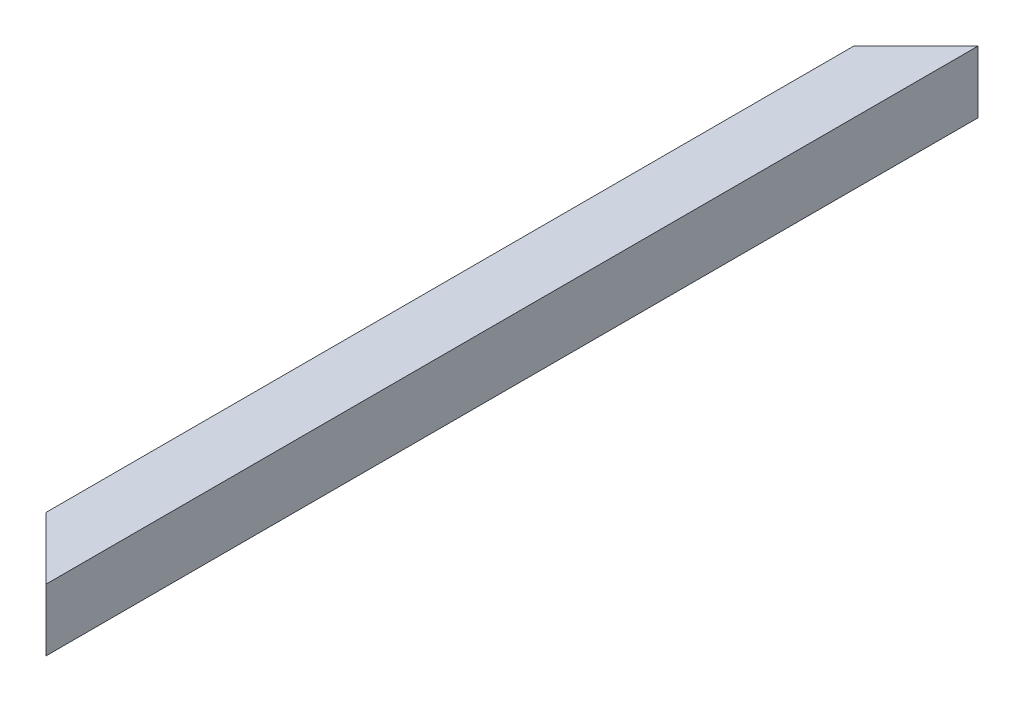
SolidWorks part; units mm, degrees
ref_plane "Front Plane" through (0, 0, 0) normal (0, 0, 1) x (1, 0, 0)
ref_plane "Top Plane" through (0, 0, 0) normal (0, 1, 0) x (1, 0, 0)
ref_plane "Right Plane" through (0, 0, 0) normal (1, 0, 0) x (0, 0, -1)
curve "Curve1"
  spline degree 1 poles (0, 0, 0) (0, 0, 900) knots 0 0 1 1
sketch "Sketch1" plane through (0, 0, 0) normal (0, 0, 1) x (1, 0, 0)
  line L0 (0, 35.3535) -> (0, -33.8384) construction
  line L1 (-30, 30) -> (30, 30)
  line L2 (-30, 30) -> (-30, -30)
  line L3 (-30, -30) -> (30, -30)
  line L4 (30, 30) -> (30, -30)
  line L5 (-26, 26) -> (26, 26)
  line L6 (-26, 26) -> (-26, -26)
  line L7 (-26, -26) -> (26, -26)
  line L8 (26, 26) -> (26, -26)
  line L9 (-39.3939, 0) -> (41.5152, 0) construction
  dimension "D1" = 60
  dimension "D2" = 52
sweep "Sweep1" add profiles "Sketch1" path "Curve1"
sketch "Sketch2" plane through (0, 30, 0) normal (0, 1, 0) x (1, 0, 0)
  line L0 (30, 0) -> (-30, -60)
  line L1 (-30, 0) -> (-30, -900) construction
  line L2 (-30, -60) -> (-30, 0)
  line L3 (-30, 0) -> (30, 0)
  line L4 (30, -900) -> (-30, -840)
  line L5 (-30, -840) -> (-30, -900)
  line L6 (-30, -900) -> (30, -900)
  dimension "D1" = 45
  dimension "D2" = 45
extrude "Cut-Extrude1" cut sketch "Sketch2" against normal through all
